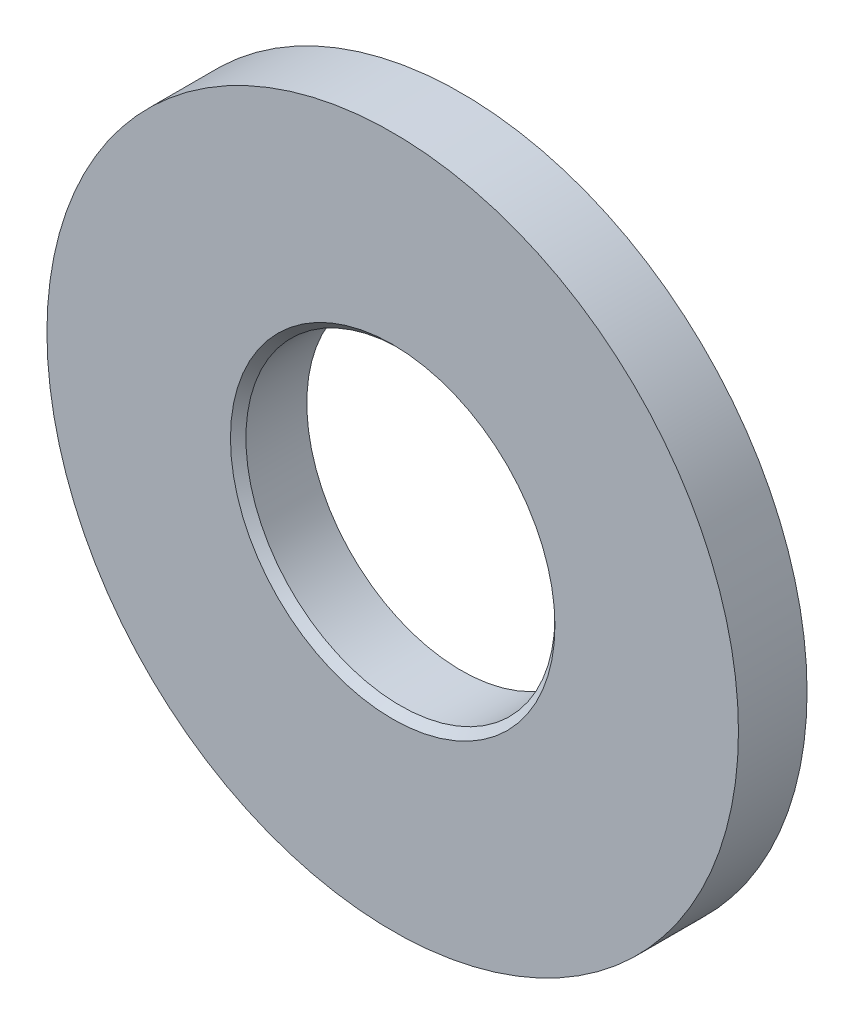
SolidWorks part; units mm, degrees
ref_plane "Front Plane" through (0, 0, 0) normal (0, 0, 1) x (1, 0, 0)
ref_plane "Top Plane" through (0, 0, 0) normal (0, 1, 0) x (1, 0, 0)
ref_plane "Right Plane" through (0, 0, 0) normal (1, 0, 0) x (0, 0, -1)
sketch "Sketch1" plane through (0, 0, 0) normal (0, 0, 1) x (1, 0, 0)
  line L0 (-8.128, 0) -> (8.128, 0) construction
  line L1 (0, -8.128) -> (0, 8.128) construction
  circle A0 centre (0, 0) radius 8.128
  circle A1 centre (0, 0) radius 3.6322
  point P4 (0, 0)
  point P9 (0, 0)
  dimension "ID" = 7.2644
  dimension "OD" = 16.256
sketch "Sketch2" plane through (0, 0, 0) normal (1, 0, 0) x (0, 0, -1)
  line L0 (0.8065, 8.128) -> (-0.8065, 8.128) construction
  line L1 (0, 8.128) -> (0, -8.128) construction
  point P4 (0, 8.128)
  dimension "Thickness" = 1.6129
sketch "Sketch3" plane through (0, 0, 0) normal (0, 0, 1) x (1, 0, 0)
  line L0 (0, -8.128) -> (0, 8.128) construction
  circle A0 centre (0, 0) radius 8.128
  circle A1 centre (0, 0) radius 3.6322
  circle A2 centre (0, 0) radius 3.6322 construction
extrude "Boss-Extrude1" add sketch "Sketch3" along normal mid plane 1.6129
chamfer "Chamfer1" distance 0.1816 angle 45 1 edges at (3.6322, 0, 0.8065)
equation "\"D1@Boss-Extrude1\" = \"Thickness@Sketch2\""
equation "\"D1@Chamfer1\"=\"ID@Sketch1\"*.025"
